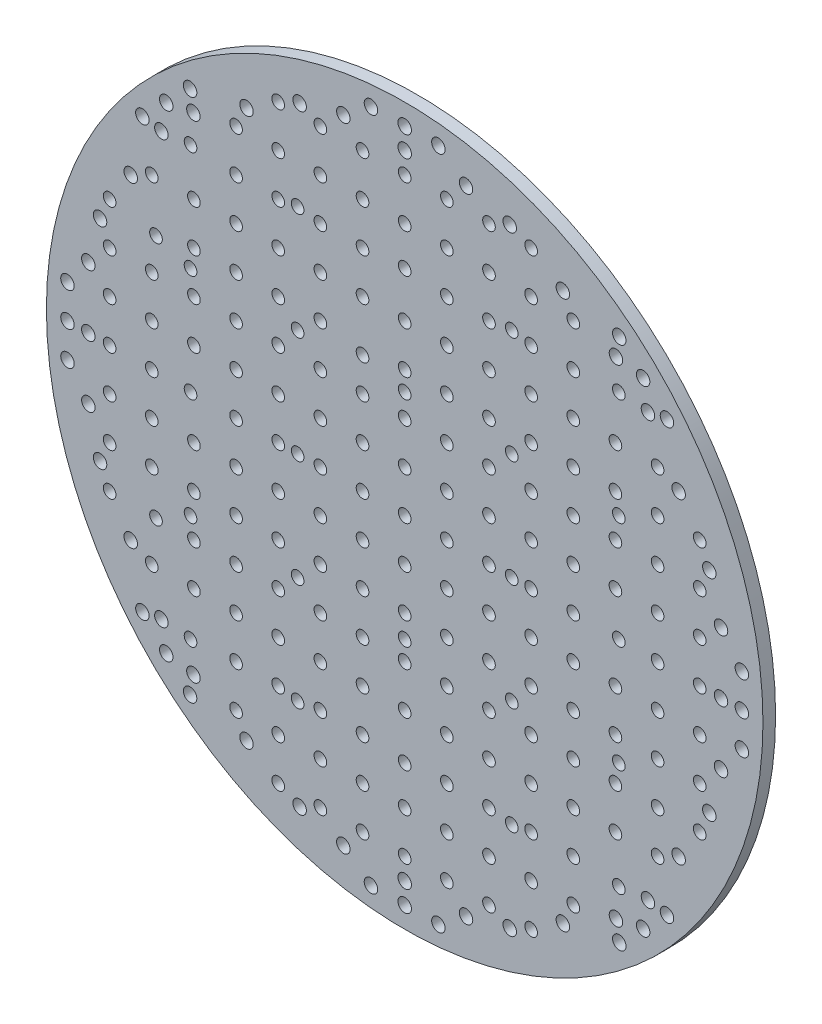
SolidWorks part; units mm, degrees
material "ABS"
ref_plane "Front" through (0, 0, 0) normal (0, 0, 1) x (1, 0, 0)
ref_plane "Top" through (0, 0, 0) normal (0, 1, 0) x (1, 0, 0)
ref_plane "Right" through (0, 0, 0) normal (1, 0, 0) x (0, 0, -1)
sketch "Эскиз1" plane through (0, 0, 0) normal (0, 0, 1) x (1, 0, 0)
  circle A342 centre (-10, 28) radius 1.5
  circle A343 centre (-59, 28) radius 1.5
  circle A344 centre (-59, -30) radius 1.5
  circle A345 centre (-10, -30) radius 1.5
  circle A346 centre (37.525, 64.9952) radius 1.6
  circle A347 centre (-50.1257, -57.7202) radius 1.6
  circle A348 centre (-57.7202, 50.1257) radius 1.6
  circle A349 centre (-24.9243, 72.2702) radius 1.6
  circle A350 centre (-75.05, 0) radius 1.6
  circle A351 centre (50.1257, -57.7202) radius 1.6
  circle A352 centre (-72.2702, 24.9243) radius 1.6
  circle A353 centre (64.9952, -37.525) radius 1.6
  circle A354 centre (50.1257, 57.7202) radius 1.6
  circle A355 centre (37.525, -64.9952) radius 1.6
  circle A356 centre (-14.55, 75.05) radius 1.6
  circle A357 centre (-72.2702, -24.9243) radius 1.6
  circle A358 centre (24.9243, -72.2702) radius 1.6
  circle A359 centre (14.55, -75.05) radius 1.6
  circle A360 centre (64.9952, 37.525) radius 1.6
  circle A361 centre (-37.525, -64.9952) radius 1.6
  circle A362 centre (-75.05, 14.55) radius 1.6
  circle A363 centre (72.2702, 24.9243) radius 1.6
  circle A364 centre (0, -75.05) radius 1.6
  circle A365 centre (-75.05, -14.55) radius 1.6
  circle A366 centre (-64.9952, 37.525) radius 1.6
  circle A367 centre (-57.7202, -50.1257) radius 1.6
  circle A368 centre (57.7202, 50.1257) radius 1.6
  circle A369 centre (-14.55, -75.05) radius 1.6
  circle A370 centre (75.05, 14.55) radius 1.6
  circle A371 centre (0, 0) radius 85
  circle A372 centre (24.9243, 72.2702) radius 1.6
  circle A373 centre (-50.1257, 57.7202) radius 1.6
  circle A374 centre (-24.9243, -72.2702) radius 1.6
  circle A375 centre (-64.9952, -37.525) radius 1.6
  circle A376 centre (75.05, -14.55) radius 1.6
  circle A377 centre (14.55, 75.05) radius 1.6
  circle A378 centre (0, 75.05) radius 1.6
  circle A379 centre (57.7202, -50.1257) radius 1.6
  circle A380 centre (75.05, 0) radius 1.6
  circle A381 centre (72.2702, -24.9243) radius 1.6
  circle A382 centre (-37.525, 64.9952) radius 1.6
  circle A383 centre (0, 0) radius 1.5
  circle A384 centre (25.4, 0) radius 1.5
  circle A385 centre (0, 25.4) radius 1.5
  circle A386 centre (25.4, 25.4) radius 1.5
  circle A387 centre (50.8, 0) radius 1.5
  circle A388 centre (50.8, 25.4) radius 1.5
  circle A389 centre (0, 50.8) radius 1.5
  circle A390 centre (25.4, 50.8) radius 1.5
  circle A391 centre (50.8, 50.8) radius 1.5
  circle A392 centre (0, -25.4) radius 1.5
  circle A393 centre (25.4, -25.4) radius 1.5
  circle A394 centre (50.8, -25.4) radius 1.5
  circle A395 centre (0, -50.8) radius 1.5
  circle A396 centre (25.4, -50.8) radius 1.5
  circle A397 centre (50.8, -50.8) radius 1.5
  circle A398 centre (0, -25.4) radius 1.5
  circle A399 centre (25.4, -25.4) radius 1.5
  circle A400 centre (50.8, -25.4) radius 1.5
  circle A401 centre (0, -50.8) radius 1.5
  circle A402 centre (25.4, -50.8) radius 1.5
  circle A403 centre (50.8, -50.8) radius 1.5
  circle A404 centre (0, 0) radius 1.5
  circle A405 centre (-25.4, 0) radius 1.5
  circle A406 centre (0, 25.4) radius 1.5
  circle A407 centre (-25.4, 25.4) radius 1.5
  circle A408 centre (-50.8, 0) radius 1.5
  circle A409 centre (-50.8, 25.4) radius 1.5
  circle A410 centre (0, 50.8) radius 1.5
  circle A411 centre (-25.4, 50.8) radius 1.5
  circle A412 centre (-50.8, 50.8) radius 1.5
  circle A413 centre (0, -25.4) radius 1.5
  circle A414 centre (-25.4, -25.4) radius 1.5
  circle A415 centre (-50.8, -25.4) radius 1.5
  circle A416 centre (0, -50.8) radius 1.5
  circle A417 centre (-25.4, -50.8) radius 1.5
  circle A418 centre (-50.8, -50.8) radius 1.5
  circle A419 centre (0, -25.4) radius 1.5
  circle A420 centre (-25.4, -25.4) radius 1.5
  circle A421 centre (-50.8, -25.4) radius 1.5
  circle A422 centre (0, -50.8) radius 1.5
  circle A423 centre (-25.4, -50.8) radius 1.5
  circle A424 centre (-50.8, -50.8) radius 1.5
  circle A425 centre (0, 0) radius 1.5
  circle A426 centre (-25.4, 0) radius 1.5
  circle A427 centre (0, 25.4) radius 1.5
  circle A428 centre (-25.4, 25.4) radius 1.5
  circle A429 centre (-50.8, 0) radius 1.5
  circle A430 centre (-50.8, 25.4) radius 1.5
  circle A431 centre (0, 50.8) radius 1.5
  circle A432 centre (-25.4, 50.8) radius 1.5
  circle A433 centre (-50.8, 50.8) radius 1.5
  circle A434 centre (0, -25.4) radius 1.5
  circle A435 centre (-25.4, -25.4) radius 1.5
  circle A436 centre (-50.8, -25.4) radius 1.5
  circle A437 centre (0, -50.8) radius 1.5
  circle A438 centre (-25.4, -50.8) radius 1.5
  circle A439 centre (-50.8, -50.8) radius 1.5
  circle A440 centre (0, -25.4) radius 1.5
  circle A441 centre (-25.4, -25.4) radius 1.5
  circle A442 centre (-50.8, -25.4) radius 1.5
  circle A443 centre (0, -50.8) radius 1.5
  circle A444 centre (-25.4, -50.8) radius 1.5
  circle A445 centre (-50.8, -50.8) radius 1.5
  circle A446 centre (0, -80) radius 1.6
  circle A447 centre (-8, -80) radius 1.6
  circle A448 centre (8, -80) radius 1.6
  circle A449 centre (0, 10) radius 1.5
  circle A450 centre (-10, 0) radius 1.5
  circle A451 centre (-10, 10) radius 1.5
  circle A452 centre (-10, 20) radius 1.5
  circle A453 centre (-10, 40) radius 1.5
  circle A454 centre (0, 20) radius 1.5
  circle A455 centre (0, 30) radius 1.5
  circle A456 centre (0, 40) radius 1.5
  circle A457 centre (0, 0) radius 1.5
  circle A458 centre (-10, 50) radius 1.5
  circle A459 centre (-10, 60) radius 1.5
  circle A460 centre (-10, 70) radius 1.5
  circle A461 centre (0, 60) radius 1.5
  circle A462 centre (0, 70) radius 1.5
  circle A463 centre (-20, 0) radius 1.5
  circle A464 centre (-20, 10) radius 1.5
  circle A465 centre (-20, 20) radius 1.5
  circle A466 centre (-20, 30) radius 1.5
  circle A467 centre (-20, 40) radius 1.5
  circle A468 centre (-20, 50) radius 1.5
  circle A469 centre (-20, 60) radius 1.5
  circle A470 centre (-20, 70) radius 1.5
  circle A471 centre (-30, 0) radius 1.5
  circle A472 centre (-30, 10) radius 1.5
  circle A473 centre (-30, 20) radius 1.5
  circle A474 centre (-30, 30) radius 1.5
  circle A475 centre (-30, 40) radius 1.5
  circle A476 centre (-30, 50) radius 1.5
  circle A477 centre (-30, 60) radius 1.5
  circle A478 centre (-30, 70) radius 1.5
  circle A479 centre (-40, 0) radius 1.5
  circle A480 centre (-40, 10) radius 1.5
  circle A481 centre (-40, 20) radius 1.5
  circle A482 centre (-40, 30) radius 1.5
  circle A483 centre (-40, 40) radius 1.5
  circle A484 centre (-40, 50) radius 1.5
  circle A485 centre (-40, 60) radius 1.5
  circle A486 centre (-50, 10) radius 1.5
  circle A487 centre (-50, 20) radius 1.5
  circle A488 centre (-50, 30) radius 1.5
  circle A489 centre (-50, 40) radius 1.5
  circle A490 centre (-60, 0) radius 1.5
  circle A491 centre (-60, 10) radius 1.5
  circle A492 centre (-60, 20) radius 1.5
  circle A493 centre (-60, 40) radius 1.5
  circle A494 centre (-70, 0) radius 1.5
  circle A495 centre (-70, 10) radius 1.5
  circle A496 centre (-70, 20) radius 1.5
  circle A497 centre (-70, 30) radius 1.5
  circle A498 centre (10, 10) radius 1.5
  circle A499 centre (10, 20) radius 1.5
  circle A500 centre (10, 30) radius 1.5
  circle A501 centre (10, 40) radius 1.5
  circle A502 centre (10, 50) radius 1.5
  circle A503 centre (10, 60) radius 1.5
  circle A504 centre (10, 70) radius 1.5
  circle A505 centre (20, 10) radius 1.5
  circle A506 centre (20, 20) radius 1.5
  circle A507 centre (20, 30) radius 1.5
  circle A508 centre (20, 40) radius 1.5
  circle A509 centre (20, 50) radius 1.5
  circle A510 centre (20, 60) radius 1.5
  circle A511 centre (20, 70) radius 1.5
  circle A512 centre (30, 10) radius 1.5
  circle A513 centre (30, 20) radius 1.5
  circle A514 centre (30, 30) radius 1.5
  circle A515 centre (30, 40) radius 1.5
  circle A516 centre (30, 50) radius 1.5
  circle A517 centre (30, 60) radius 1.5
  circle A518 centre (30, 70) radius 1.5
  circle A519 centre (40, 10) radius 1.5
  circle A520 centre (40, 20) radius 1.5
  circle A521 centre (40, 30) radius 1.5
  circle A522 centre (40, 40) radius 1.5
  circle A523 centre (40, 50) radius 1.5
  circle A524 centre (40, 60) radius 1.5
  circle A525 centre (50, 10) radius 1.5
  circle A526 centre (50, 20) radius 1.5
  circle A527 centre (50, 30) radius 1.5
  circle A528 centre (50, 40) radius 1.5
  circle A529 centre (60, 10) radius 1.5
  circle A530 centre (60, 20) radius 1.5
  circle A531 centre (60, 30) radius 1.5
  circle A532 centre (60, 40) radius 1.5
  circle A533 centre (70, 10) radius 1.5
  circle A534 centre (70, 20) radius 1.5
  circle A535 centre (70, 30) radius 1.5
  circle A536 centre (10, 0) radius 1.5
  circle A537 centre (20, 0) radius 1.5
  circle A538 centre (30, 0) radius 1.5
  circle A539 centre (40, 0) radius 1.5
  circle A540 centre (60, 0) radius 1.5
  circle A541 centre (70, 0) radius 1.5
  circle A542 centre (0, -10) radius 1.5
  circle A543 centre (-10, -10) radius 1.5
  circle A544 centre (-10, -20) radius 1.5
  circle A545 centre (-10, -40) radius 1.5
  circle A546 centre (0, -20) radius 1.5
  circle A547 centre (0, -30) radius 1.5
  circle A548 centre (0, -40) radius 1.5
  circle A549 centre (-10, -50) radius 1.5
  circle A550 centre (-10, -60) radius 1.5
  circle A551 centre (-10, -70) radius 1.5
  circle A552 centre (0, -60) radius 1.5
  circle A553 centre (0, -70) radius 1.5
  circle A554 centre (-20, -10) radius 1.5
  circle A555 centre (-20, -20) radius 1.5
  circle A556 centre (-20, -30) radius 1.5
  circle A557 centre (-20, -40) radius 1.5
  circle A558 centre (-20, -50) radius 1.5
  circle A559 centre (-20, -60) radius 1.5
  circle A560 centre (-20, -70) radius 1.5
  circle A561 centre (-30, -10) radius 1.5
  circle A562 centre (-30, -20) radius 1.5
  circle A563 centre (-30, -30) radius 1.5
  circle A564 centre (-30, -40) radius 1.5
  circle A565 centre (-30, -50) radius 1.5
  circle A566 centre (-30, -60) radius 1.5
  circle A567 centre (-30, -70) radius 1.5
  circle A568 centre (-40, -10) radius 1.5
  circle A569 centre (-40, -20) radius 1.5
  circle A570 centre (-40, -30) radius 1.5
  circle A571 centre (-40, -40) radius 1.5
  circle A572 centre (-40, -50) radius 1.5
  circle A573 centre (-40, -60) radius 1.5
  circle A574 centre (-50, -10) radius 1.5
  circle A575 centre (-50, -20) radius 1.5
  circle A576 centre (-50, -30) radius 1.5
  circle A577 centre (-50, -40) radius 1.5
  circle A578 centre (-60, -10) radius 1.5
  circle A579 centre (-60, -20) radius 1.5
  circle A580 centre (-60, -40) radius 1.5
  circle A581 centre (-70, -10) radius 1.5
  circle A582 centre (-70, -20) radius 1.5
  circle A583 centre (-70, -30) radius 1.5
  circle A584 centre (10, -10) radius 1.5
  circle A585 centre (10, -20) radius 1.5
  circle A586 centre (10, -30) radius 1.5
  circle A587 centre (10, -40) radius 1.5
  circle A588 centre (10, -50) radius 1.5
  circle A589 centre (10, -60) radius 1.5
  circle A590 centre (10, -70) radius 1.5
  circle A591 centre (20, -10) radius 1.5
  circle A592 centre (20, -20) radius 1.5
  circle A593 centre (20, -30) radius 1.5
  circle A594 centre (20, -40) radius 1.5
  circle A595 centre (20, -50) radius 1.5
  circle A596 centre (20, -60) radius 1.5
  circle A597 centre (20, -70) radius 1.5
  circle A598 centre (30, -10) radius 1.5
  circle A599 centre (30, -20) radius 1.5
  circle A600 centre (30, -30) radius 1.5
  circle A601 centre (30, -40) radius 1.5
  circle A602 centre (30, -50) radius 1.5
  circle A603 centre (30, -60) radius 1.5
  circle A604 centre (30, -70) radius 1.5
  circle A605 centre (40, -10) radius 1.5
  circle A606 centre (40, -20) radius 1.5
  circle A607 centre (40, -30) radius 1.5
  circle A608 centre (40, -40) radius 1.5
  circle A609 centre (40, -50) radius 1.5
  circle A610 centre (40, -60) radius 1.5
  circle A611 centre (50, -10) radius 1.5
  circle A612 centre (50, -20) radius 1.5
  circle A613 centre (50, -30) radius 1.5
  circle A614 centre (50, -40) radius 1.5
  circle A615 centre (60, -10) radius 1.5
  circle A616 centre (60, -20) radius 1.5
  circle A617 centre (60, -30) radius 1.5
  circle A618 centre (60, -40) radius 1.5
  circle A619 centre (70, -10) radius 1.5
  circle A620 centre (70, -20) radius 1.5
  circle A621 centre (70, -30) radius 1.5
  circle A622 centre (56.5685, -56.5685) radius 1.6
  circle A623 centre (50.9117, -62.2254) radius 1.6
  circle A624 centre (62.2254, -50.9117) radius 1.6
  circle A625 centre (80, 0) radius 1.6
  circle A626 centre (80, -8) radius 1.6
  circle A627 centre (80, 8) radius 1.6
  circle A628 centre (56.5685, 56.5685) radius 1.6
  circle A629 centre (62.2254, 50.9117) radius 1.6
  circle A630 centre (50.9117, 62.2254) radius 1.6
  circle A631 centre (0, 80) radius 1.6
  circle A632 centre (8, 80) radius 1.6
  circle A633 centre (-8, 80) radius 1.6
  circle A634 centre (-56.5685, 56.5685) radius 1.6
  circle A635 centre (-50.9117, 62.2254) radius 1.6
  circle A636 centre (-62.2254, 50.9117) radius 1.6
  circle A637 centre (-80, 0) radius 1.6
  circle A638 centre (-80, 8) radius 1.6
  circle A639 centre (-80, -8) radius 1.6
  circle A640 centre (-56.5685, -56.5685) radius 1.6
  circle A641 centre (-62.2254, -50.9117) radius 1.6
  circle A642 centre (-50.9117, -62.2254) radius 1.6
extrude "Бобышка-Вытянуть1" add sketch "Эскиз1" along normal blind 3
